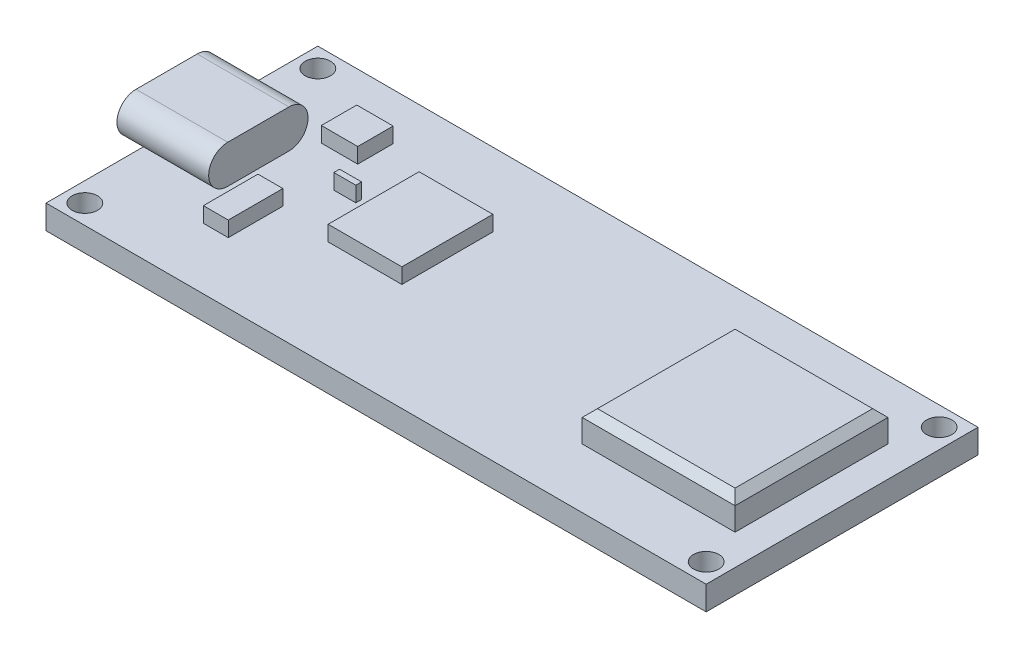
SolidWorks part; units mm, degrees
ref_plane "Front Plane" through (0, 0, 0) normal (0, 0, 1) x (1, 0, 0)
ref_plane "Top Plane" through (0, 0, 0) normal (0, 1, 0) x (1, 0, 0)
ref_plane "Right Plane" through (0, 0, 0) normal (1, 0, 0) x (0, 0, -1)
sketch "Sketch1" plane through (0, 0, 0) normal (0, 1, 0) x (1, 0, 0)
  line L1 (21.59, -8.89) -> (-21.59, -8.89)
  line L2 (21.59, -8.89) -> (21.59, 8.89)
  line L3 (21.59, 8.89) -> (-21.59, 8.89)
  line L4 (-21.59, -8.89) -> (-21.59, 8.89)
  line L5 (21.59, -8.89) -> (-21.59, 8.89) construction
  line L6 (21.59, 8.89) -> (-21.59, -8.89) construction
  line L7 (20.32, -7.62) -> (-20.32, -7.62) construction
  line L8 (20.32, -7.62) -> (20.32, 7.62) construction
  line L9 (20.32, 7.62) -> (-20.32, 7.62) construction
  line L10 (-20.32, -7.62) -> (-20.32, 7.62) construction
  line L11 (20.32, -7.62) -> (-20.32, 7.62) construction
  line L12 (20.32, 7.62) -> (-20.32, -7.62) construction
  circle A0 centre (-20.32, 7.62) radius 0.83
  circle A1 centre (20.32, 7.62) radius 0.83
  circle A2 centre (20.32, -7.62) radius 0.83
  circle A3 centre (-20.32, -7.62) radius 0.83
  point P0 (0, 0)
  point P6 (0, 0)
  dimension "D5" = 1.66
  dimension "D1" = 43.18
  dimension "D2" = 17.78
  dimension "D3" = 15.24
  dimension "D4" = 40.64
extrude "Boss-Extrude1" add sketch "Sketch1" along normal blind 1.57
sketch "Sketch2" plane through (0, 1.57, 0) normal (0, 1, 0) x (1, 0, 0)
  line L0 (21.59, -8.89) -> (21.59, 8.89) construction
  line L1 (19.59, -5) -> (9.59, -5)
  line L2 (19.59, -5) -> (19.59, 5)
  line L3 (19.59, 5) -> (9.59, 5)
  line L4 (9.59, -5) -> (9.59, 5)
  line L5 (19.59, -5) -> (9.59, 5) construction
  line L6 (19.59, 5) -> (9.59, -5) construction
  point P0 (14.59, 0)
  point P5 (0, 0)
  dimension "D1" = 10
  dimension "D2" = 10
  dimension "D3" = 2
extrude "Boss-Extrude2" add sketch "Sketch2" along normal blind 2
chamfer "Chamfer1" distance 0.5 angle 45 4 edges at (14.59, 3.57, -5) (19.59, 3.57, 0) (9.59, 3.57, 0) (14.59, 3.57, 5)
sketch "Sketch3" plane through (-21.59, 0, 0) normal (-1, 0, 0) x (0, 0, 1)
  line L0 (-2, 2.82) -> (2, 2.82) construction
  line L1 (-2, 4.07) -> (2, 4.07)
  line L2 (-2, 1.57) -> (2, 1.57)
  line L3 (-8.89, 1.57) -> (8.89, 1.57) construction
  arc A0 (-2, 4.07) -> (-2, 1.57) centre (-2, 2.82) ccw
  arc A1 (2, 1.57) -> (2, 4.07) centre (2, 2.82) ccw
  point P2 (0, 2.82)
  point P7 (0, 0)
  dimension "D1" = 4
  dimension "D2" = 2.5
extrude "Boss-Extrude3" add sketch "Sketch3" along normal blind 1 and the other way blind 5
sketch "Sketch4" plane through (0, 1.57, 0) normal (0, 1, 0) x (1, 0, 0)
  line L1 (-15.9791, 5.8262) -> (-13.5989, 5.8262)
  line L2 (-15.9791, 5.8262) -> (-15.9791, 3.5086)
  line L3 (-15.9791, 3.5086) -> (-13.5989, 3.5086)
  line L4 (-13.5989, 5.8262) -> (-13.5989, 3.5086)
  line L5 (-15.9791, 5.8262) -> (-13.5989, 3.5086) construction
  line L6 (-15.9791, 3.5086) -> (-13.5989, 5.8262) construction
  line L7 (-15.2951, -1.3204) -> (-13.6665, -1.3204)
  line L8 (-15.2951, -1.3204) -> (-15.2951, -4.8907)
  line L9 (-15.2951, -4.8907) -> (-13.6665, -4.8907)
  line L10 (-13.6665, -1.3204) -> (-13.6665, -4.8907)
  line L11 (-15.2951, -1.3204) -> (-13.6665, -4.8907) construction
  line L12 (-15.2951, -4.8907) -> (-13.6665, -1.3204) construction
  line L13 (-10.1618, 4.0858) -> (-5.3387, 4.0858)
  line L14 (-10.1618, 4.0858) -> (-10.1618, -1.8648)
  line L15 (-10.1618, -1.8648) -> (-5.3387, -1.8648)
  line L16 (-5.3387, 4.0858) -> (-5.3387, -1.8648)
  line L17 (-10.1618, 4.0858) -> (-5.3387, -1.8648) construction
  line L18 (-10.1618, -1.8648) -> (-5.3387, 4.0858) construction
  line L19 (-11.4692, 1.6295) -> (-12.9099, 1.6295)
  line L20 (-11.4692, 1.6295) -> (-11.4692, 1.2537)
  line L21 (-11.4692, 1.2537) -> (-12.9099, 1.2537)
  line L22 (-12.9099, 1.6295) -> (-12.9099, 1.2537)
  line L23 (-11.4692, 1.6295) -> (-12.9099, 1.2537) construction
  line L24 (-11.4692, 1.2537) -> (-12.9099, 1.6295) construction
  point P0 (-14.789, 4.6674)
  point P5 (-14.4808, -3.1056)
  point P10 (-7.7502, 1.1105)
  point P15 (-12.1895, 1.4416)
extrude "Boss-Extrude4" add sketch "Sketch4" along normal blind 1
